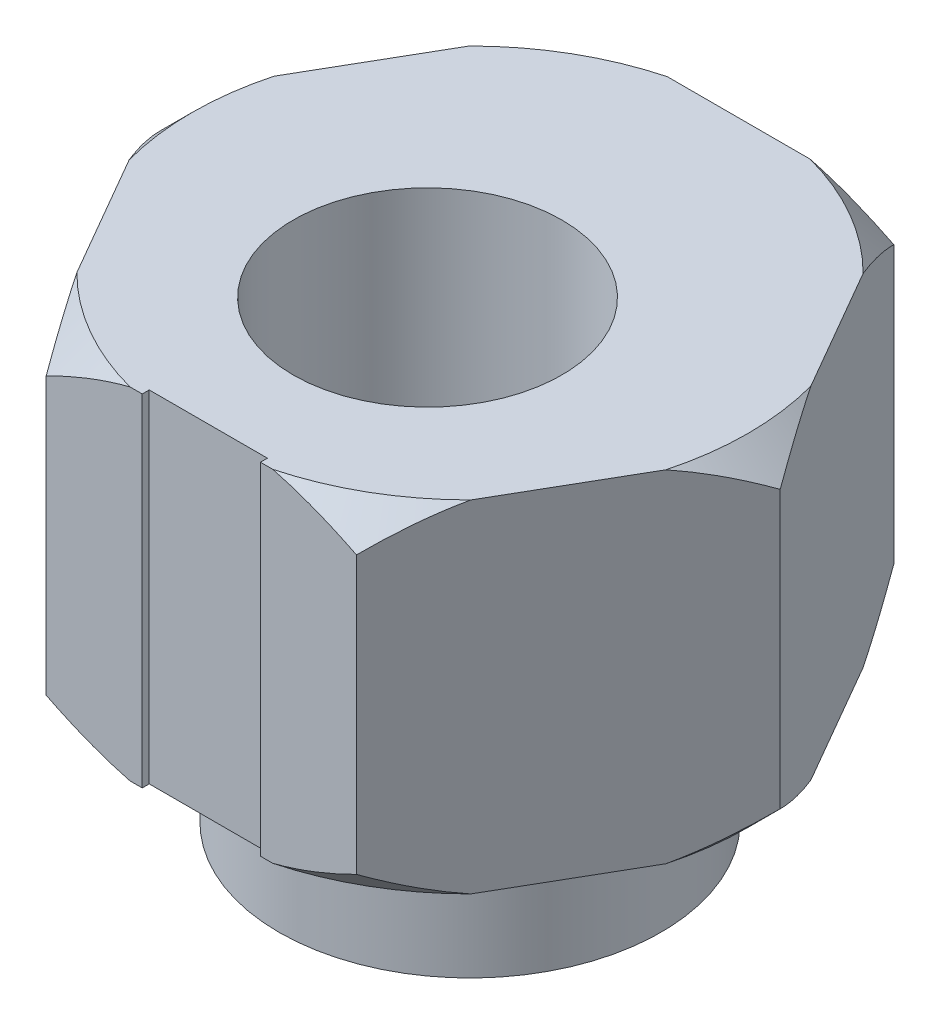
SolidWorks part; units mm, degrees
material "AISI 304"
ref_plane "Front Plane" through (0, 0, 0) normal (0, 0, 1) x (1, 0, 0)
ref_plane "Top Plane" through (0, 0, 0) normal (0, 1, 0) x (1, 0, 0)
ref_plane "Right Plane" through (0, 0, 0) normal (1, 0, 0) x (0, 0, -1)
sketch "Sketch1" plane through (0, 0, 0) normal (0, 1, 0) x (1, 0, 0)
  line L1 (5.7735, 0) -> (2.8868, 5)
  line L2 (2.8868, 5) -> (-2.8868, 5)
  line L3 (-2.8868, 5) -> (-5.7735, 0)
  line L4 (-5.7735, 0) -> (-2.8868, -5)
  line L5 (-2.8868, -5) -> (2.8868, -5)
  line L6 (2.8868, -5) -> (5.7735, 0)
  circle A0 centre (0, 0) radius 5 construction
  dimension "D1" = 10
extrude "Boss-Extrude1" add sketch "Sketch1" along normal blind 6.35
sketch "Sketch3" plane through (0, 0, 0) normal (0, -1, 0) x (1, 0, 0)
  circle A0 centre (0, 0) radius 3.555
  dimension "D1" = 7.11
extrude "Boss-Extrude3" add sketch "Sketch3" along normal blind 2.5
sketch "Sketch4" plane through (0, 6.35, 0) normal (0, 1, 0) x (1, 0, 0)
  line L0 (0, 0) -> (0, -0.79) construction
  circle A0 centre (0, -0.79) radius 2.5
  dimension "D1" = 5
  dimension "D2" = 0.79
extrude "Cut-Extrude1" cut sketch "Sketch4" against normal through all
sketch "Sketch5" plane through (0, 0, 0) normal (0, -1, 0) x (-1, 0, 0)
  line L0 (2.8868, -5) -> (-2.8868, -5) construction
  line L1 (-1.1, -5) -> (1.1, -5)
  line L2 (-1.1, -5) -> (-1.1, -4.87)
  line L3 (-1.1, -4.87) -> (1.1, -4.87)
  line L4 (1.1, -5) -> (1.1, -4.87)
  line L5 (0, -5) -> (0, 0) construction
  dimension "D1" = 2.2
  dimension "D2" = 0.13
extrude "Cut-Extrude2" cut sketch "Sketch5" against normal through all
sketch "Sketch6" plane through (0, 0, 0) normal (0, 0, 1) x (1, 0, 0)
  line L0 (0, 0) -> (0, 6.4706) construction
  line L1 (5.1735, 6.35) -> (5.7735, 6.35)
  line L2 (2.8868, 6.35) -> (5.7735, 6.35) construction
  line L3 (5.7735, 6.35) -> (5.7735, 5.75)
  line L4 (5.7735, 6.35) -> (5.7735, 0) construction
  line L5 (5.7735, 5.75) -> (5.1735, 6.35)
  line L6 (5.7735, 3.175) -> (6.8775, 3.175) construction
  line L7 (5.7735, 6.35) -> (5.7735, 0) construction
  line L8 (5.7735, 0.6) -> (5.1735, 0)
  line L9 (5.7735, 0) -> (5.7735, 0.6)
  line L10 (5.1735, 0) -> (5.7735, 0)
  dimension "D1" = 0.6
revolve "Cut-Revolve1" cut sketch "Sketch6" angle 360 about L0
